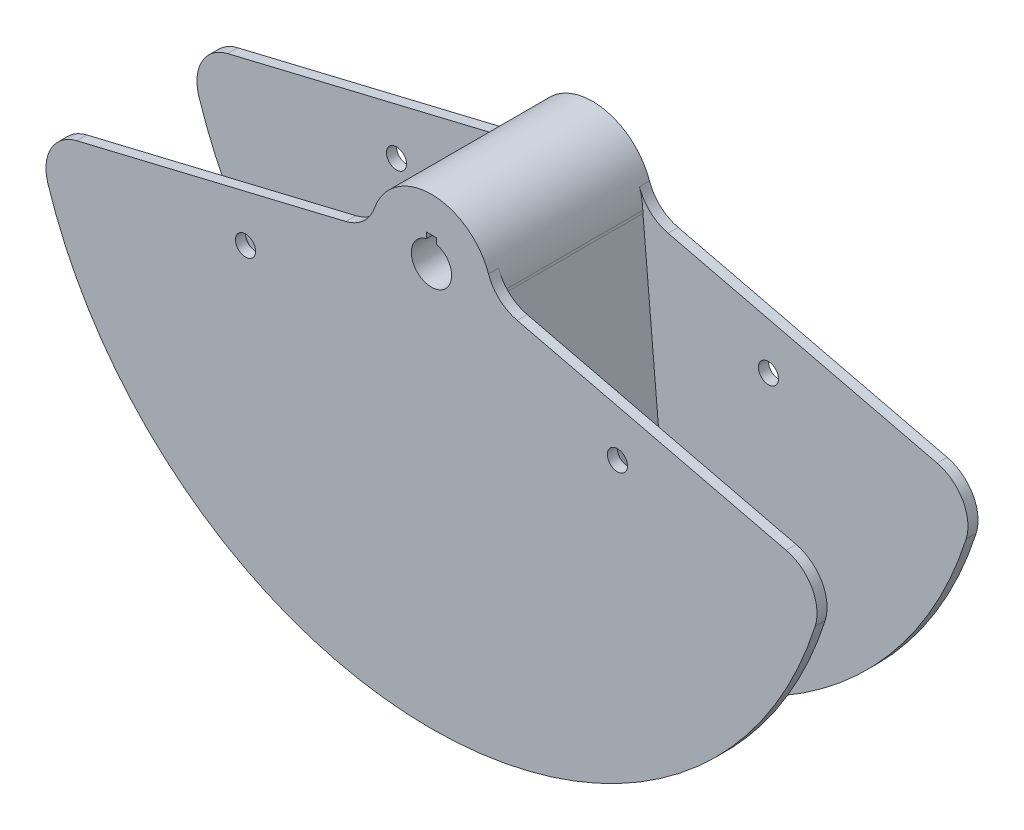
SolidWorks part; units mm, degrees
material "AISI 1020"
ref_plane "Front Plane" through (0, 0, 0) normal (0, 0, 1) x (1, 0, 0)
ref_plane "Top Plane" through (0, 0, 0) normal (0, 1, 0) x (1, 0, 0)
ref_plane "Right Plane" through (0, 0, 0) normal (1, 0, 0) x (0, 0, -1)
other "Center of Mass"
sketch "Sketch1" plane through (0, 0, 0) normal (0, 0, 1) x (1, 0, 0)
  line L0 (-59.6996, -246.8845) -> (-38.1844, -0.9642)
  line L1 (-38.1, 0) -> (38.1, 0) construction
  line L2 (38.1844, -0.9642) -> (59.6996, -246.8845)
  line L3 (0, 0) -> (-117.3327, -48.6008) construction
  line L4 (0, 0) -> (0, -254) construction
  line L5 (117.3327, -48.6008) -> (0, 0) construction
  arc A0 (-59.6996, -246.8845) -> (59.6996, -246.8845) centre (0, 0) ccw
  circle A1 centre (0, 0) radius 127 construction
  circle A2 centre (0, 0) radius 12.7
  arc A3 (38.0926, 0.7497) -> (-38.0926, 0.7497) centre (0, 0) ccw
  circle A4 centre (-117.3327, -48.6008) radius 12.7 construction
  circle A5 centre (117.3327, -48.6008) radius 12.7 construction
  arc A6 (38.1844, -0.9642) -> (38.0926, 0.7497) centre (63.4877, 1.2495) cw
  arc A7 (-38.1844, -0.9642) -> (-38.0926, 0.7497) centre (-63.4877, 1.2495) ccw
  dimension "D1" = 508
  dimension "D2" = 254
  dimension "D3" = 25.4
  dimension "D4" = 25.4
  dimension "D5" = 25.4
  dimension "D8" = 25.4
  dimension "D6" = 135
  dimension "D7" = 67.5
  dimension "D9" = 10
extrude "Boss-Extrude1" add sketch "Sketch1" along normal mid plane 88.9
sketch "Sketch5" plane through (0, 0, 44.45) normal (0, 0, 1) x (1, 0, 0)
  line L0 (-223.7799, -44.5778) -> (-54.0427, -3.8275)
  line L1 (-38.1, 0) -> (38.1, 0) construction
  line L2 (54.0427, -3.8275) -> (223.7799, -44.5778)
  line L3 (0, 0) -> (-117.3327, -48.6008) construction
  line L4 (0, 0) -> (0, -254) construction
  line L5 (117.3327, -48.6008) -> (0, 0) construction
  line L6 (-117.3327, -48.6008) -> (117.3327, -48.6008) construction
  arc A0 (-242.056, -76.9733) -> (242.056, -76.9733) centre (0, 0) ccw
  circle A2 centre (0, 0) radius 12.7
  arc A3 (35.9833, 12.5224) -> (-35.9833, 12.5224) centre (0, 0) ccw
  circle A4 centre (-117.3327, -48.6008) radius 6.35
  circle A5 centre (117.3327, -48.6008) radius 6.35
  arc A6 (54.0427, -3.8275) -> (35.9833, 12.5224) centre (59.9722, 20.8707) cw
  arc A7 (-54.0427, -3.8275) -> (-35.9833, 12.5224) centre (-59.9722, 20.8707) ccw
  arc A8 (-223.7799, -44.5778) -> (-242.056, -76.9733) centre (-217.8504, -69.276) ccw
  arc A9 (223.7799, -44.5778) -> (242.056, -76.9733) centre (217.8504, -69.276) cw
  dimension "D1" = 508
  dimension "D2" = 153
  dimension "D3" = 25.4
  dimension "D5" = 12.7
  dimension "D8" = 25.4
  dimension "D4" = 25.4
  dimension "D10" = 25.4
  dimension "D6" = 135
  dimension "D9" = 127
extrude "Boss-Extrude2" add sketch "Sketch5" along normal blind 6.35
sketch "Sketch6" plane through (0, 0, -44.45) normal (0, 0, -1) x (-1, 0, 0)
  line L0 (-222.4045, -51.6882) -> (-53.3494, -4.2767)
  line L1 (-38.1, 0) -> (38.1, 0) construction
  line L2 (53.3494, -4.2767) -> (222.4045, -51.6882)
  line L3 (0, 0) -> (-117.3327, -48.6008) construction
  line L4 (0, 0) -> (0, -254) construction
  line L5 (117.3327, -48.6008) -> (0, 0) construction
  arc A0 (-239.4952, -84.6052) -> (239.4952, -84.6052) centre (0, 0) ccw
  circle A1 centre (0, 0) radius 127 construction
  circle A2 centre (0, 0) radius 12.7
  arc A3 (36.1249, 12.1078) -> (-36.1249, 12.1078) centre (0, 0) ccw
  circle A4 centre (-117.3327, -48.6008) radius 6.35
  circle A5 centre (117.3327, -48.6008) radius 6.35
  arc A6 (53.3494, -4.2767) -> (36.1249, 12.1078) centre (60.2082, 20.1797) cw
  arc A7 (-53.3494, -4.2767) -> (-36.1249, 12.1078) centre (-60.2082, 20.1797) ccw
  arc A8 (222.4045, -51.6882) -> (239.4952, -84.6052) centre (215.5457, -76.1446) cw
  arc A9 (-222.4045, -51.6882) -> (-239.4952, -84.6052) centre (-215.5457, -76.1446) ccw
  dimension "D1" = 508
  dimension "D2" = 254
  dimension "D3" = 25.4
  dimension "D4" = 12.7
  dimension "D7" = 25.4
  dimension "D9" = 25.4
  dimension "D10" = 25.4
  dimension "D5" = 135
  dimension "D6" = 67.5
  dimension "D8" = 25.4
extrude "Boss-Extrude4" [suppressed] add sketch "Sketch6" along normal blind 6.35
mirror "Mirror1" about plane through (0, 0, 0) normal (0, 0, 1) of "Boss-Extrude2"
sketch "Sketch8" plane through (0, 0, 0) normal (0, 0, 1) x (1, 0, 0)
  line L0 (0, 0) -> (0, 12.7) construction
  line L2 (3.175, 9.525) -> (-3.175, 9.525)
  line L3 (3.175, 9.525) -> (3.175, 15.875)
  line L4 (3.175, 15.875) -> (-3.175, 15.875)
  line L5 (-3.175, 9.525) -> (-3.175, 15.875)
  line L6 (3.175, 9.525) -> (-3.175, 15.875) construction
  line L7 (3.175, 15.875) -> (-3.175, 9.525) construction
  circle A0 centre (0, 0) radius 12.7 construction
  arc A1 (3.175, 12.2967) -> (-3.175, 12.2967) centre (0, 0) ccw
  dimension "D1" = 6.35
  dimension "D2" = 6.35
extrude "Cut-Extrude1" cut sketch "Sketch8" against normal through all both and the other way through all contours L3 L4 L5 L2
